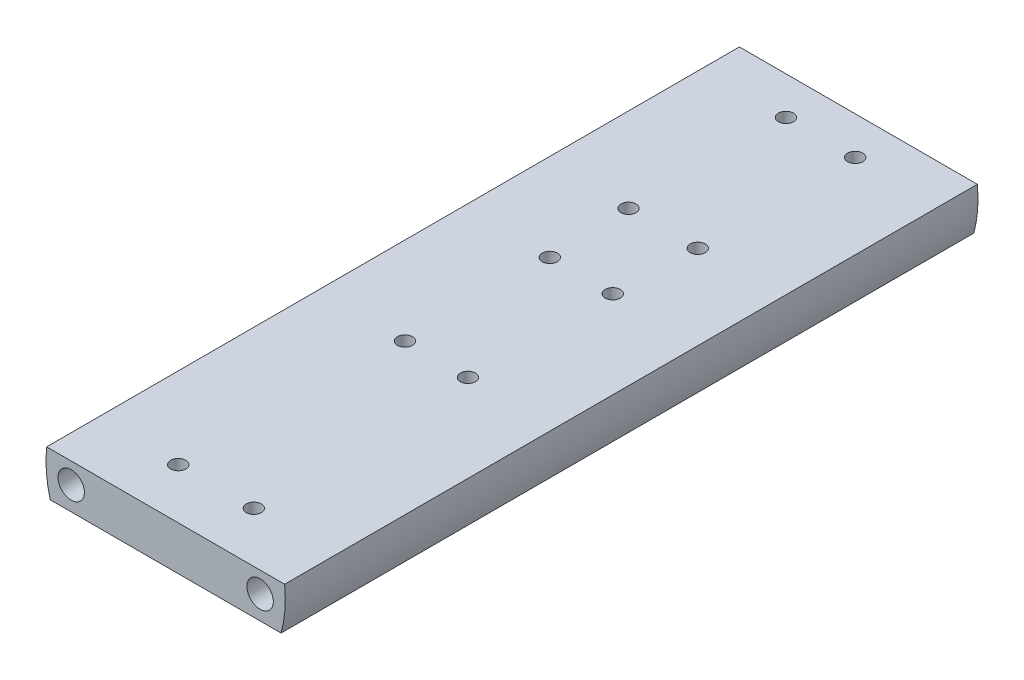
SolidWorks part; units mm, degrees
ref_plane "Front Plane" through (0, 0, 0) normal (0, 0, 1) x (1, 0, 0)
ref_plane "Top Plane" through (0, 0, 0) normal (0, 1, 0) x (1, 0, 0)
ref_plane "Right Plane" through (0, 0, 0) normal (1, 0, 0) x (0, 0, -1)
sketch "Sketch1" plane through (0, 0, 0) normal (0, 0, 1) x (1, 0, 0)
  line L0 (0, 0) -> (48.26, 0)
  line L1 (0, 2.54) -> (48.26, 2.54)
  line L2 (0, -6.35) -> (48.26, -6.35)
  circle A0 centre (24.13, 0) radius 24.13
  circle A1 centre (5.08, -1.6349) radius 2.667
  circle A2 centre (43.18, -1.6349) radius 2.667
  dimension "D3" = 5.334
  dimension "D4" = 19.05
  dimension "D6" = 48.26
  dimension "D1" = 2.54
  dimension "D2" = 6.35
  dimension "D5" = 2
extrude "Boss-Extrude1" add sketch "Sketch1" along normal blind 139.7 contours L0 A0 L1 | L0 A0
sketch "Sketch2" plane through (0, 2.54, 0) normal (0, 1, 0) x (1, 0, 0)
  line L0 (0.1341, 0) -> (48.1259, 0) construction
  circle A0 centre (17.145, -7.62) radius 1.524
  circle A1 centre (31.115, -7.62) radius 1.524
  circle A2 centre (31.115, -39.37) radius 1.524
  circle A3 centre (17.145, -39.37) radius 1.524
  circle A4 centre (17.78, -55.88) radius 1.524
  circle A5 centre (30.48, -55.88) radius 1.524
  circle A6 centre (30.48, -85.09) radius 1.524
  circle A7 centre (17.78, -85.09) radius 1.524
  circle A8 centre (16.51, -129.54) radius 1.524
  circle A9 centre (31.75, -129.54) radius 1.524
  point P4 (24.13, 0)
  dimension "D1" = 3.048
  dimension "D2" = 7.62
  dimension "D3" = 6.985
  dimension "D6" = 3.048
  dimension "D7" = 6.35
  dimension "D8" = 55.88
  dimension "D11" = 3.048
  dimension "D12" = 44.45
  dimension "D13" = 1.27
  dimension "D4" = 2
  dimension "D5" = 2
  dimension "D9" = 2
  dimension "D10" = 2
  dimension "D14" = 2
extrude "Cut-Extrude1" cut sketch "Sketch2" against normal blind 5.08
sketch "Sketch5" plane through (0, -6.35, 0) normal (0, -1, 0) x (1, 0, 0)
  line L0 (0.8505, 139.7) -> (47.4095, 139.7) construction
  circle A0 centre (17.78, 125.73) radius 1.524
  circle A1 centre (30.48, 125.73) radius 1.524
  circle A2 centre (30.48, 100.33) radius 1.524
  circle A3 centre (17.78, 100.33) radius 1.524
  dimension "D1" = 3.048
  dimension "D2" = 17.78
  dimension "D5" = 13.97
  dimension "D3" = 2
  dimension "D4" = 2
extrude "Cut-Extrude2" cut sketch "Sketch5" against normal blind 5.08
